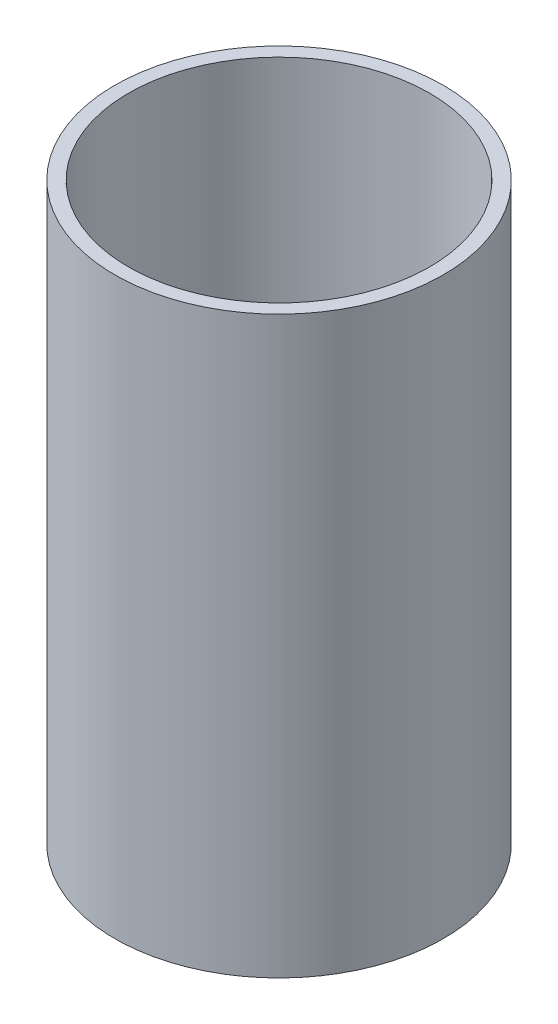
SolidWorks part; units mm, degrees
ref_plane "Front Plane" through (0, 0, 0) normal (0, 0, 1) x (1, 0, 0)
ref_plane "Top Plane" through (0, 0, 0) normal (0, 1, 0) x (1, 0, 0)
ref_plane "Right Plane" through (0, 0, 0) normal (1, 0, 0) x (0, 0, -1)
sketch "Sketch1" plane through (0, 0, 0) normal (0, 0, 1) x (1, 0, 0)
  line L0 (0, 0) -> (0, 55.0613) construction
  line L2 (11, 0) -> (12, 0)
  line L3 (11, 0) -> (11, 42)
  line L4 (11, 42) -> (12, 42)
  line L5 (12, 0) -> (12, 42)
  dimension "D1" = 42
  dimension "D2" = 11
  dimension "D3" = 12
revolve "Revolve1" add sketch "Sketch1" angle 360 about L0
